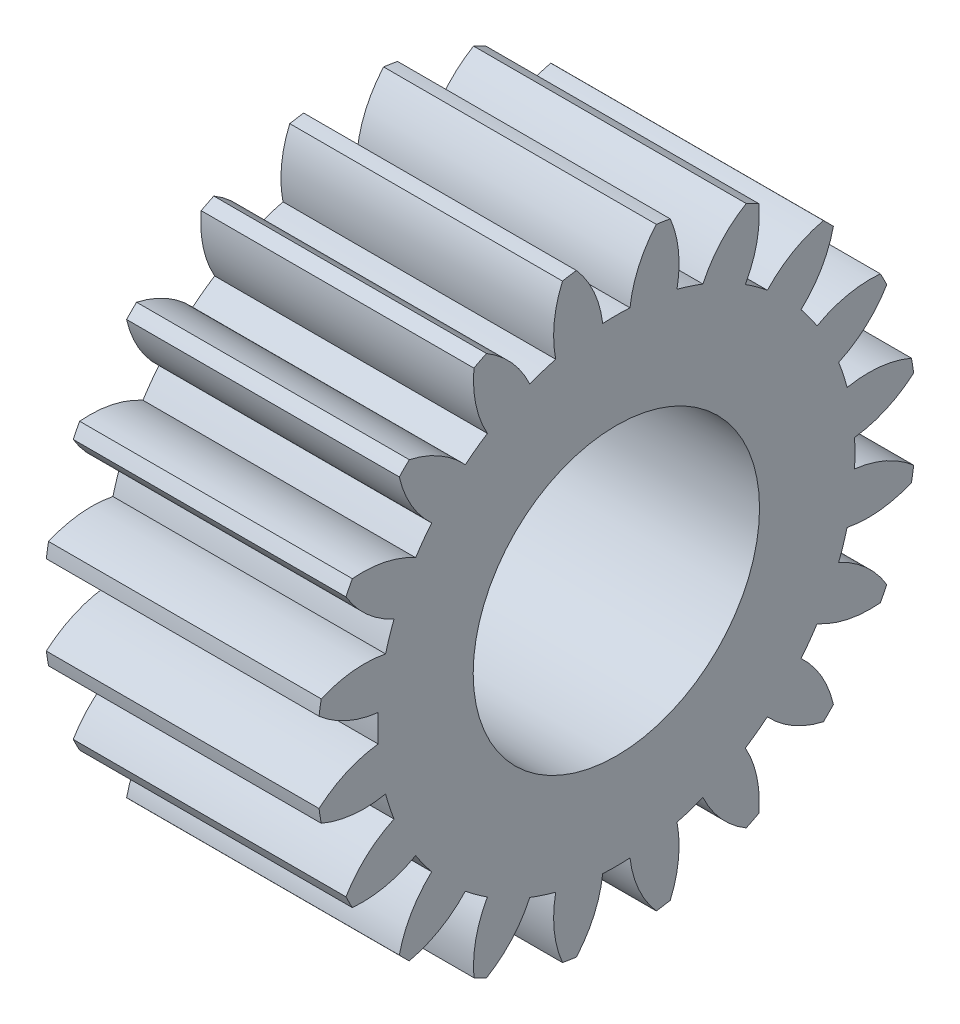
SolidWorks part; units mm, degrees
ref_plane "Plane1" through (0, 0, 0) normal (0, 0, 1) x (1, 0, 0)
ref_plane "Plane2" through (0, 0, 0) normal (0, 1, 0) x (1, 0, 0)
ref_plane "Plane3" through (0, 0, 0) normal (1, 0, 0) x (0, 0, -1)
sketch "HoldingSke" plane through (0, 0, 0) normal (0, 1, 0) x (1, 0, 0)
  line L0 (0, 0) -> (0.9397, -0.342)
  line L1 (-15, 0) -> (100, 0) construction
  line L2 (0, 0) -> (-2.1039, 2.3779)
  line L3 (0, 0) -> (-11.863, 4.5341)
  line L4 (0, 0) -> (8.1152, 2.9537)
  line L5 (0, 0) -> (-46.8476, -17.4728)
  line L6 (0, 0) -> (-8.2896, -5.593)
  line L7 (-2.1039, 2.3779) -> (8.6586, 51.2059)
  line L8 (-76.2, 54.61) -> (-76.1, 54.61)
  line L9 (-71.009, 38.7566) -> (-53.1078, 45.2721)
  line L10 (-76.2, 71.12) -> (104.1128, 71.12)
  line L11 (0, 0) -> (-10, 0)
  line L12 (-76.2, 101.6) -> (-76.162, 101.6)
  line L13 (24.9733, 27.94) -> (52.9518, 28.4284)
  line L14 (24.9733, 27.94) -> (24.9743, 27.94)
  line L15 (24.9733, 27.94) -> (100.4006, 29.5858)
  line L16 (-63.627, -1) -> (-12.827, -1)
  circle A0 centre (0, 0) radius 0.4
  circle A1 centre (0, 0) radius 8.749
  circle A2 centre (0, 0) radius 37.5
  circle A3 centre (0, 0) radius 0.4
  dimension "MHD" = 17.498
  dimension "Hub_dia" = 75
  dimension "Bore" = 0.8
  dimension "MBD" = 0.8
  dimension "Num_teeth" = 20
  dimension "Pitch" = 1
  dimension "Overall_len" = 50
  dimension "Show_teeth" = 20
  dimension "Thickness" = 10
  dimension "OAL" = 50.0001
  dimension "T_dim" = 0.1
  dimension "Ap" = 20
  dimension "H" = 19.05
  dimension "Pitch_radius" = 180.3128
  dimension "Width" = 10
  dimension "Backlash" = 0.038
  dimension "Addendum_fac" = 1
  dimension "Dedendum_fac" = 1.25
  dimension "Clearance_fac" = 0.25
  dimension "Dedendum_add" = 0.001
  dimension "Module" = 1
sketch "BasProSke" plane through (0, 0, 0) normal (0, 1, 0) x (1, 0, 0)
  line L0 (-10, 0) -> (60, 0) construction
  line L1 (0, 0) -> (0, 11)
  line L2 (0, 0) -> (10, 0)
  line L3 (10, 0) -> (10, 11)
  line L4 (10, 11) -> (0, 11)
  dimension "Thickness" = 10
  dimension "Diameter" = 22
revolve "Base-Revolve" add sketch "BasProSke" angle 360 about L0
sketch "TooCutSke" plane through (0, 0, 0) normal (1, 0, 0) x (0, 0, -1)
  line L1 (0, 0) -> (0, 107) construction
  line L2 (0, 0) -> (-0.8511, 9.9637) construction
  line L3 (0, 0) -> (-3.1206, 19.7028) construction
  line L4 (-0.8511, 9.9637) -> (-1.5603, 9.8514) construction
  arc A0 (0.4999, 8.7347) -> (-0.4999, 8.7347) centre (0, 0) ccw
  arc A1 (1.4852, 10.9249) -> (-1.4852, 10.9249) centre (0, 0) ccw
  circle A2 centre (0, 0) radius 10 construction
  circle A3 centre (0, 0) radius 9.3969 construction
  arc A4 (-0.4999, 8.7347) -> (-1.4852, 10.9249) centre (-4.4722, 8.2645) ccw
  arc A5 (1.4852, 10.9249) -> (0.4999, 8.7347) centre (4.4722, 8.2645) ccw
  dimension "Root_dia" = 17.498
  dimension "Overcut_dia" = 22.0508
  dimension "Pitch_dia" = 20
  dimension "Base_dia" = 18.7939
  dimension "Flank_rad" = 4
  dimension "Half_ang" = 9
  dimension "Half_CT" = 0.7181
extrude "ToothCut" cut sketch "TooCutSke" along normal through all
fillet "Breaks" [suppressed] radius 0.02
fillet "RootFillets" [suppressed] radius 0.251
pattern_circular "TeethCuts" count 20 every 18 about axis through (-10, 0, 0) along (1, 0, 0) of "ToothCut", "RootFillets", "Breaks"
sketch "HubNeaOneSke" plane through (0, 0, 0) normal (-1, 0, 0) x (0, 0, 1)
  circle A0 centre (0, 0) radius 8.749
  dimension "Diameter" = 17.498
extrude "HubNearOne" [suppressed] add sketch "HubNeaOneSke" along normal blind 40.0001
sketch "HubNeaBotSke" plane through (0, 0, 0) normal (-1, 0, 0) x (0, 0, 1)
  circle A0 centre (0, 0) radius 8.749
  dimension "Diameter" = 17.498
extrude "HubNearBoth" [suppressed] add sketch "HubNeaBotSke" along normal blind 20
ref_plane "FarPln" through (10, 0, 0) normal (1, 0, 0) x (0, 0, -1)
sketch "HubFarSke" plane through (10, 0, 0) normal (1, 0, 0) x (0, 0, -1)
  circle A0 centre (0, 0) radius 8.749
  dimension "Diameter" = 17.498
extrude "HubFar" [suppressed] add sketch "HubFarSke" along normal blind 20
sketch "BorSke" plane through (0, 0, 0) normal (1, 0, 0) x (0, 0, -1)
  circle A0 centre (0, 0) radius 0.4
  dimension "Diameter" = 0.8
extrude "Bore" cut sketch "BorSke" along normal mid plane 100.0001
sketch "KeySke" plane through (0, 0, 0) normal (1, 0, 0) x (0, 0, -1)
  line L0 (-0.05, 0) -> (-0.05, 0.5)
  line L1 (-0.05, 0.5) -> (0.05, 0.5)
  line L2 (0.05, 0.5) -> (0.05, 0)
  line L3 (0, 0) -> (0, 34) construction
  line L4 (-0.05, 0) -> (0.05, 0)
  dimension "Offset" = 0.5
  dimension "Width" = 0.1
extrude "Keyway" [suppressed] cut sketch "KeySke" along normal mid plane 100.0001
pattern_circular "Keyway2" [suppressed] count 2 every 90 about axis through (-10, 0, 0) along (1, 0, 0)
hole_wizard "Taladro de margen para M101" positions "Croquis1" profile "Croquis2" hole size "M10" standard "ISO" end condition through all
sketch "Croquis1" plane through (10, 0, 0) normal (1, 0, 0) x (0, 0, -1)
  point P0 (0, 0)
sketch "Croquis2" plane through (10, 0, 0) normal (0, 1, 0) x (0, 0, -1)
  line L0 (0, 0) -> (0, 10)
  line L1 (0, 10) -> (5.25, 10)
  line L2 (5.25, 10) -> (5.25, 0)
  line L5 (5.25, 0) -> (0, 0)
  line L11 (0, -6.35) -> (0, 107.95) construction
  dimension "Diámetro de taladro hasta el siguiente" = 10.5
  dimension "Profundidad de taladro hasta el siguiente" = 10
equation "' \"Module@HoldingSke\" = 6.35"
equation "' \"Num_teeth@HoldingSke\" = 12"
equation "' \"Ap@HoldingSke\" =  20"
equation "' \"Ap@HoldingSke\" = 20"
equation "' \"Width@HoldingSke\" = 0.5 * 25.4"
equation "' \"Hub_dia@HoldingSke\"= 1 * 25.4"
equation "' \"Hub_dia@HoldingSke\" = 1 * 25.4"
equation "' \"Overall_len@HoldingSke\" = 1.0 * 25.4"
equation "' \"Bore@HoldingSke\" = 0.75 * 25.4"
equation "' \"T_dim@HoldingSke\" = 0.1 * 25.4"
equation "' \"Width@KeySke\" = 0.25 * 25.4"
equation "' \"Show_teeth@HoldingSke\" = 13"
equation "' \"Backlash@HoldingSke\" = 0.009 * 25.4"
equation "' \"Addendum_fac@HoldingSke\" = 1.0"
equation "' \"Dedendum_fac@HoldingSke\" = 1.25"
equation "' \"Dedendum_add@HoldingSke\" = 0.00005 * 25.4"
equation "' \"Clearance_fac@HoldingSke\" = 0.25"
equation "\"Pitch@HoldingSke\" = 1 / \"Module@HoldingSke\""
equation "\"Overcut_dia@TooCutSke\" = (\"Num_teeth@HoldingSke\" + 2 * \"Addendum_fac@HoldingSke\") / \"Pitch@HoldingSke\" + 0.002 * 25.4"
equation "\"Pitch_dia@TooCutSke\" = \"Num_teeth@HoldingSke\" / \"Pitch@HoldingSke\""
equation "\"Base_dia@TooCutSke\" = \"Num_teeth@HoldingSke\" / \"Pitch@HoldingSke\" * cos((\"Ap@HoldingSke\"  * 3.14159265 / 180))"
equation "\"Root_dia@TooCutSke\" = (\"Num_teeth@HoldingSke\" + 2) / \"Pitch@HoldingSke\" - 2 * (\"Addendum_fac@HoldingSke\" + \"Dedendum_fac@HoldingSke\") / \"Pitch@HoldingSke\" - \"Dedendum_add@HoldingSke\" * 2"
equation "\"Half_ang@TooCutSke\" = 180 / \"Num_teeth@HoldingSke\""
equation "\"Half_CT@TooCutSke\" = \"Num_teeth@HoldingSke\" / \"Pitch@HoldingSke\" * sin((3.14159265 / 2 / \"Num_teeth@HoldingSke\")) / 2 - 7 * \"Backlash@HoldingSke\" / 4"
equation "\"Flank_rad@TooCutSke\" = \"Num_teeth@HoldingSke\" / \"Pitch@HoldingSke\" / 5"
equation "\"Radius@RootFillets\" = \"Clearance_fac@HoldingSke\" / \"Pitch@HoldingSke\" + \"Dedendum_add@HoldingSke\""
equation "\"Break_rad@Breaks\" = 0.02 / \"Pitch@HoldingSke\""
equation "\"Thickness@HoldingSke\" = \"Width@HoldingSke\""
equation "\"OAL@HoldingSke\" = \"Thickness@HoldingSke\""
equation "\"MHD@HoldingSke\" = (\"Num_teeth@HoldingSke\" + 2) / \"Pitch@HoldingSke\" - 2 * (\"Addendum_fac@HoldingSke\" + \"Dedendum_fac@HoldingSke\")  / \"Pitch@HoldingSke\" - \"Dedendum_add@HoldingSke\" * 2"
equation "\"MBD@HoldingSke\" = (\"Num_teeth@HoldingSke\" + 2) / \"Pitch@HoldingSke\" - 2 * (\"Addendum_fac@HoldingSke\" + \"Dedendum_fac@HoldingSke\")  / \"Pitch@HoldingSke\" - \"Dedendum_add@HoldingSke\" * 2 - 0.002 * 25.4"
equation "\"MHD@HoldingSke\" = ((sgn( \"MHD@HoldingSke\" - \"Hub_dia@HoldingSke\" )-1)*( \"MHD@HoldingSke\" - \"Hub_dia@HoldingSke\" ))/-2+ \"Hub_dia@HoldingSke\""
equation "\"MBD@HoldingSke\" = ((sgn( \"MBD@HoldingSke\" - \"Bore@HoldingSke\" )-1)*( \"MBD@HoldingSke\" - \"Bore@HoldingSke\" ))/-2+ \"Bore@HoldingSke\""
equation "\"OAL@HoldingSke\" = ((sgn( \"OAL@HoldingSke\" - \"Overall_len@HoldingSke\" )+1)*( \"OAL@HoldingSke\" - \"Overall_len@HoldingSke\" ))/2 + \"Overall_len@HoldingSke\" + 0.000002 * 25.4"
equation "\"Num_teeth@TeethCuts\" = int( \"Show_teeth@HoldingSke\" ) + 1"
equation "\"Num_teeth@TeethCuts\" = ((sgn( \"Num_teeth@TeethCuts\" - \"Num_teeth@HoldingSke\" )-1)*( \"Num_teeth@TeethCuts\" - \"Num_teeth@HoldingSke\" ))/-2+ \"Num_teeth@HoldingSke\""
equation "\"Num_teeth@TeethCuts\" = ((sgn( \"Num_teeth@TeethCuts\" - 2.0)+1)*( \"Num_teeth@TeethCuts\" - 2.0))/2 +2.0"
equation "\"Angle@TeethCuts\" = 360.0 / \"Num_teeth@HoldingSke\""
equation "\"Diameter@BasProSke\" = (\"Num_teeth@HoldingSke\" + 2 * \"Addendum_fac@HoldingSke\") / \"Pitch@HoldingSke\""
equation "\"Thickness@BasProSke\"  = \"Thickness@HoldingSke\""
equation "' \"Fillet_rad@BasProSke\" =  \"Thickness@HoldingSke\" * 0.05"
equation "' \"Fillet_rad@BasProSke\" = \"Thickness@HoldingSke\" * 0.05"
equation "\"MHD@HoldingSke\" = ((sgn( \"MHD@HoldingSke\" - \"Root_dia@TooCutSke\" )-1)*( \"MHD@HoldingSke\" - \"Root_dia@TooCutSke\" ))/-2+ \"Root_dia@TooCutSke\""
equation "\"Diameter@HubNeaOneSke\" = \"MHD@HoldingSke\""
equation "\"Length@HubNearOne\" = \"OAL@HoldingSke\" - \"Thickness@BasProSke\""
equation "\"Diameter@HubNeaBotSke\" = \"MHD@HoldingSke\""
equation "\"Length@HubNearBoth\" = ( \"OAL@HoldingSke\" - \"Thickness@BasProSke\" ) / 2.0"
equation "\"Thickness@FarPln\" = \"Thickness@BasProSke\""
equation "\"Diameter@HubFarSke\" = \"MHD@HoldingSke\""
equation "\"Length@HubFar\" = ( \"OAL@HoldingSke\" - \"Thickness@BasProSke\" ) / 2.0"
equation "\"Diameter@BorSke\" = \"MBD@HoldingSke\""
equation "\"D1@Bore\" = \"OAL@HoldingSke\" * 2.0"
equation "\"D1@Keyway\" = \"OAL@HoldingSke\" * 2.0"
equation "\"Offset@KeySke\" = \"T_dim@HoldingSke\" + \"MBD@HoldingSke\" / 2.0"
